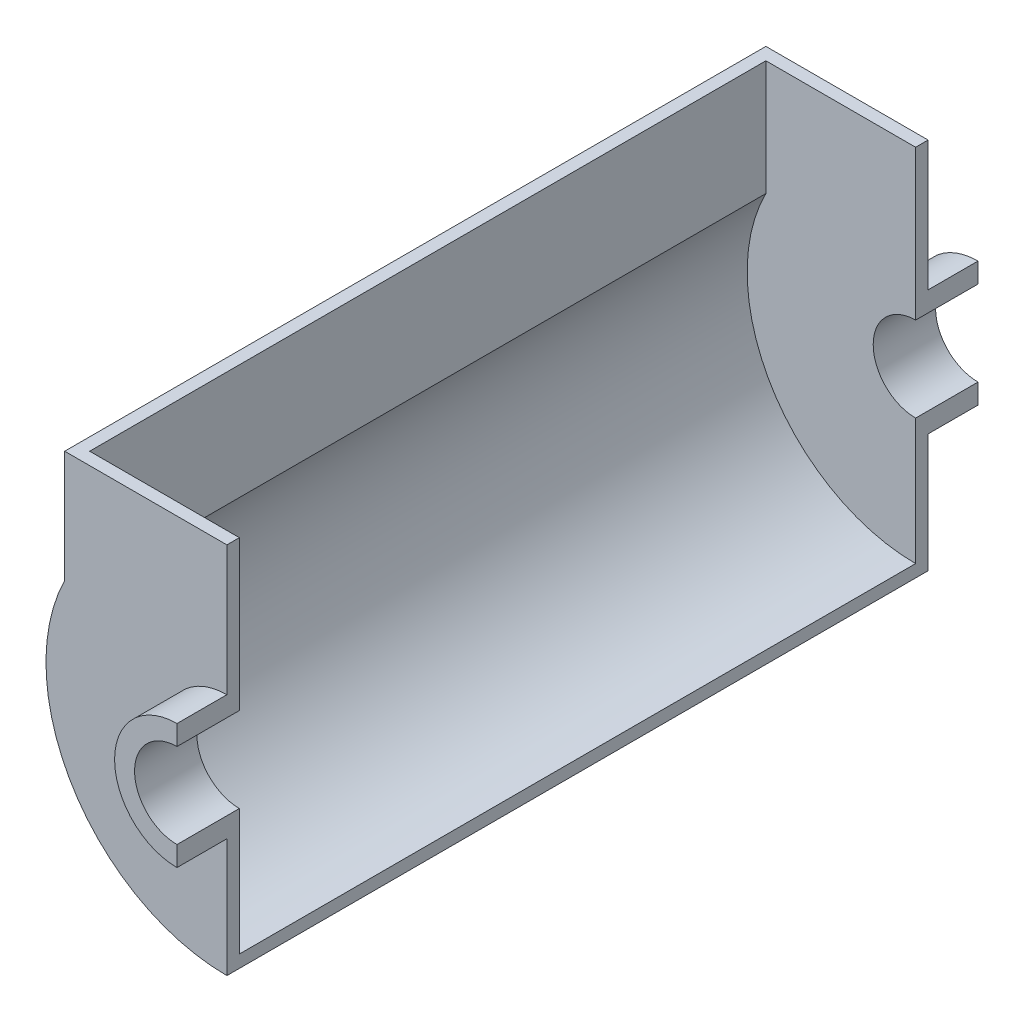
SolidWorks part; units mm, degrees
ref_plane "Front Plane" through (0, 0, 0) normal (0, 0, 1) x (1, 0, 0)
ref_plane "Top Plane" through (0, 0, 0) normal (0, 1, 0) x (1, 0, 0)
ref_plane "Right Plane" through (0, 0, 0) normal (1, 0, 0) x (0, 0, -1)
sketch "Sketch1" plane through (0, 0, 0) normal (0, 0, 1) x (1, 0, 0)
  line L0 (0, 25) -> (0, 17)
  line L1 (0, -17) -> (0, -25)
  arc A0 (0, 25) -> (0, -25) centre (0, 0) ccw
  arc A1 (0, 17) -> (0, -17) centre (0, 0) ccw
  dimension "D1" = 50
  dimension "D2" = 34
extrude "Boss-Extrude1" add sketch "Sketch1" along normal blind 20 and the other way blind 5
sketch "Sketch2" plane through (0, 0, 0) normal (0, 0, 1) x (1, 0, 0)
  line L0 (0, 25) -> (0, 77)
  line L1 (0, 77) -> (-65, 77)
  line L2 (-65, 77) -> (-65, 32.1131)
  line L3 (0, -25) -> (0, -72.5)
  arc A0 (0, 25) -> (0, -25) centre (0, 0) ccw construction
  arc A1 (0, 25) -> (0, -25) centre (0, 0) ccw
  arc A2 (-65, 32.1131) -> (0, -72.5) centre (0, 0) ccw
  point P9 (0, 0)
  dimension "D3" = 72.5
  dimension "D1" = 52
  dimension "D2" = 65
extrude "Boss-Extrude2" add sketch "Sketch2" against normal blind 5
ref_plane "Plane2" through (0, 0, -140.5) normal (0, 0, 1) x (1, 0, 0)
mirror "Mirror5" about plane through (0, 0, -140.5) normal (0, 0, 1) of bodies 102
sketch "Sketch3" plane through (0, 0, -5) normal (0, 0, -1) x (-1, 0, 0)
  line L0 (65, 77) -> (65, 32.1131) construction
  line L1 (65, 77) -> (65, 32.1131)
  line L2 (60, 77) -> (60, 30.9233)
  line L3 (65, 77) -> (60, 77)
  line L4 (0, -72.5) -> (0, -67.5)
  arc A0 (0, -72.5) -> (65, 32.1131) centre (0, 0) ccw construction
  arc A1 (0, -72.5) -> (65, 32.1131) centre (0, 0) ccw
  arc A2 (0, -67.5) -> (60, 30.9233) centre (0, 0) ccw
  dimension "D1" = 5
extrude "Boss-Extrude3" add sketch "Sketch3" along normal up to surface (271 mm away) contours L2 A2 L4 A1 L1 L3
